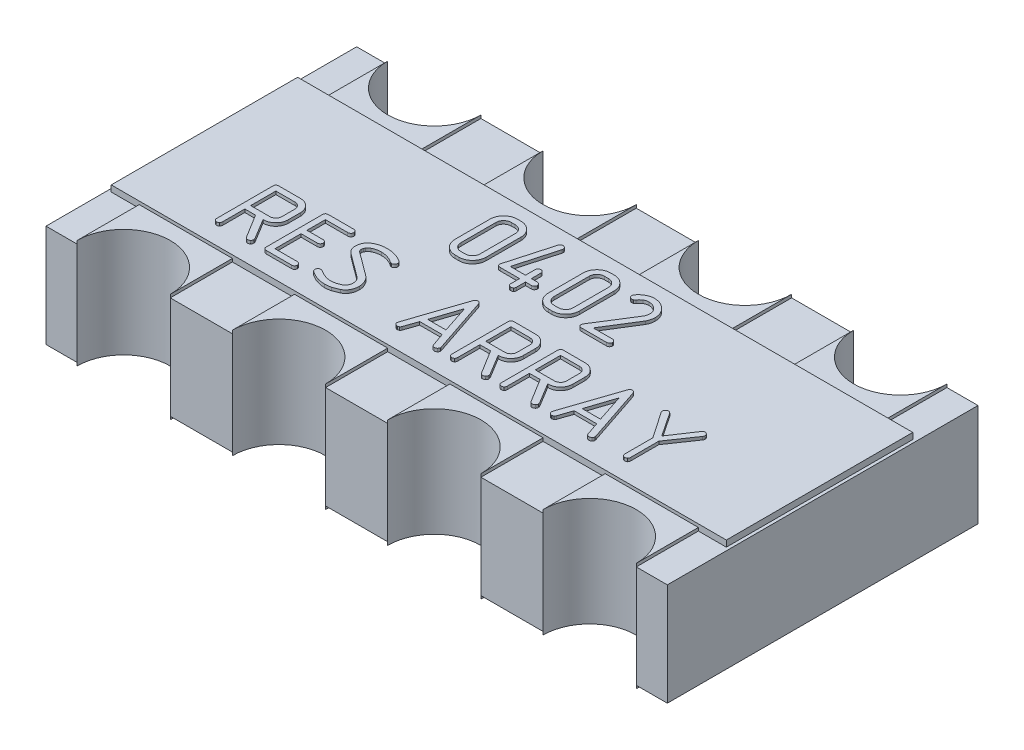
SolidWorks part; units mm, degrees
ref_plane "Спереди" through (0, 0, 0) normal (0, 0, 1) x (1, 0, 0)
ref_plane "Сверху" through (0, 0, 0) normal (0, 1, 0) x (1, 0, 0)
ref_plane "Справа" through (0, 0, 0) normal (1, 0, 0) x (0, 0, -1)
sketch "Эскиз1" plane through (0, 0, 0) normal (0, 1, 0) x (1, 0, 0)
  line L1 (-1, 0.5) -> (1, 0.5)
  line L2 (-1, 0.5) -> (-1, -0.5)
  line L3 (-1, -0.5) -> (1, -0.5)
  line L4 (1, 0.5) -> (1, -0.5)
  line L5 (-1, 0.5) -> (1, -0.5) construction
  line L6 (-1, -0.5) -> (1, 0.5) construction
  dimension "D1" = 2
  dimension "D2" = 1
extrude "Body" add sketch "Эскиз1" along normal blind 0.33
sketch "Эскиз9" plane through (0, 0.33, 0) normal (0, 1, 0) x (1, 0, 0)
  line L1 (-0.9, -0.2) -> (-0.6, -0.2)
  line L2 (-0.9, -0.2) -> (-0.9, -0.5)
  line L3 (-0.9, -0.5) -> (-0.6, -0.5)
  line L4 (-0.6, -0.2) -> (-0.6, -0.5)
  line L5 (-1, -0.5) -> (1, -0.5) construction
  line L6 (-1, 0.5) -> (-1, -0.5) construction
  line L7 (-0.4, -0.2) -> (-0.1, -0.2)
  line L8 (-0.4, -0.2) -> (-0.4, -0.5)
  line L9 (-0.4, -0.5) -> (-0.1, -0.5)
  line L10 (-0.1, -0.2) -> (-0.1, -0.5)
  line L11 (0.1, -0.2) -> (0.4, -0.2)
  line L12 (0.1, -0.2) -> (0.1, -0.5)
  line L13 (0.1, -0.5) -> (0.4, -0.5)
  line L14 (0.4, -0.2) -> (0.4, -0.5)
  line L15 (0.6, -0.2) -> (0.9, -0.2)
  line L16 (0.6, -0.2) -> (0.6, -0.5)
  line L17 (0.6, -0.5) -> (0.9, -0.5)
  line L18 (0.9, -0.2) -> (0.9, -0.5)
  line L19 (0, 0) -> (1.0621, 0) construction
  line L20 (0.9, 0.2) -> (0.9, 0.5)
  line L21 (0.6, 0.5) -> (0.9, 0.5)
  line L22 (0.6, 0.2) -> (0.6, 0.5)
  line L23 (0.6, 0.2) -> (0.9, 0.2)
  line L24 (0.4, 0.2) -> (0.4, 0.5)
  line L25 (0.1, 0.5) -> (0.4, 0.5)
  line L26 (0.1, 0.2) -> (0.1, 0.5)
  line L27 (0.1, 0.2) -> (0.4, 0.2)
  line L28 (-0.1, 0.2) -> (-0.1, 0.5)
  line L29 (-0.4, 0.5) -> (-0.1, 0.5)
  line L30 (-0.4, 0.2) -> (-0.4, 0.5)
  line L31 (-0.4, 0.2) -> (-0.1, 0.2)
  line L32 (-0.6, 0.2) -> (-0.6, 0.5)
  line L33 (-0.9, 0.5) -> (-0.6, 0.5)
  line L34 (-0.9, 0.2) -> (-0.9, 0.5)
  line L35 (-0.9, 0.2) -> (-0.6, 0.2)
  dimension "D1" = 0.3
  dimension "D2" = 0.1
  dimension "D4" = 0.3
  dimension "D3" = 4
extrude "Pads" add sketch "Эскиз9" along normal blind 0.01 and the other way blind 0.34
sketch "Эскиз10" plane through (0, 0.34, 0) normal (0, 1, 0) x (1, 0, 0)
  line L0 (-0.9, -0.5) -> (-0.6, -0.5)
  line L1 (-0.4, -0.5) -> (-0.1, -0.5)
  line L2 (0.1, -0.5) -> (0.4, -0.5)
  line L3 (0.6, -0.5) -> (0.9, -0.5)
  line L4 (0, 0) -> (1.1518, 0) construction
  line L5 (0.6, 0.5) -> (0.9, 0.5)
  line L6 (0.1, 0.5) -> (0.4, 0.5)
  line L7 (-0.4, 0.5) -> (-0.1, 0.5)
  line L8 (-0.9, 0.5) -> (-0.6, 0.5)
  arc A0 (-0.9, -0.5) -> (-0.6, -0.5) centre (-0.75, -0.5) cw
  arc A1 (-0.4, -0.5) -> (-0.1, -0.5) centre (-0.25, -0.5) cw
  arc A2 (0.1, -0.5) -> (0.4, -0.5) centre (0.25, -0.5) cw
  arc A3 (0.6, -0.5) -> (0.9, -0.5) centre (0.75, -0.5) cw
  arc A4 (0.6, 0.5) -> (0.9, 0.5) centre (0.75, 0.5) ccw
  arc A5 (0.1, 0.5) -> (0.4, 0.5) centre (0.25, 0.5) ccw
  arc A6 (-0.4, 0.5) -> (-0.1, 0.5) centre (-0.25, 0.5) ccw
  arc A7 (-0.9, 0.5) -> (-0.6, 0.5) centre (-0.75, 0.5) ccw
extrude "holes" cut sketch "Эскиз10" against normal through all
sketch "Эскиз11" plane through (0, 0.33, 0) normal (0, 1, 0) x (1, 0, 0)
  line L1 (-0.99, 0.3) -> (0.99, 0.3)
  line L2 (-0.99, 0.3) -> (-0.99, -0.3)
  line L3 (-0.99, -0.3) -> (0.99, -0.3)
  line L4 (0.99, 0.3) -> (0.99, -0.3)
  line L5 (-0.99, 0.3) -> (0.99, -0.3) construction
  line L6 (-0.99, -0.3) -> (0.99, 0.3) construction
  point P0 (0, 0)
  dimension "D1" = 1.98
  dimension "D2" = 0.6
extrude "text_plane" add sketch "Эскиз11" along normal blind 0.02
sketch "Эскиз12" plane through (0, 0.35, 0) normal (0, 1, 0) x (1, 0, 0)
  line L0 (-0.294, 0.0481) -> (0.2935, 0.0481) construction
  line L1 (-0.7358, -0.2432) -> (0.8329, -0.2432) construction
  text T0 "0402" font "GOST type B" height 0.2
  text T1 "RES ARRAY" font "GOST type B" height 0.2
extrude "text" add sketch "Эскиз12" along normal blind 0.01
